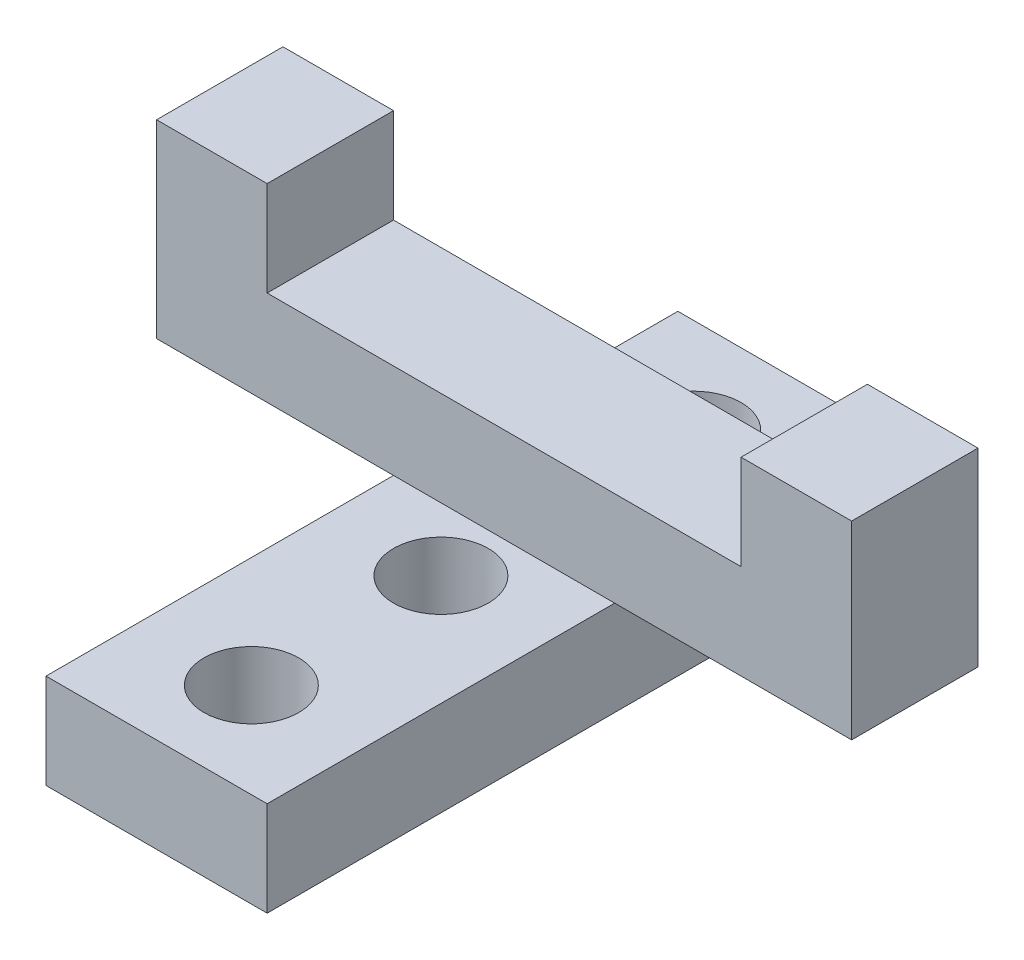
SolidWorks part; units mm, degrees
ref_plane "Front Plane" through (0, 0, 0) normal (0, 0, 1) x (1, 0, 0)
ref_plane "Top Plane" through (0, 0, 0) normal (0, 1, 0) x (1, 0, 0)
ref_plane "Right Plane" through (0, 0, 0) normal (1, 0, 0) x (0, 0, -1)
sketch "Sketch2" plane through (0, 0, 0) normal (0, 1, 0) x (1, 0, 0)
  line L1 (-3.5, -10) -> (3.5, -10)
  line L2 (-3.5, -10) -> (-3.5, 10)
  line L3 (-3.5, 10) -> (3.5, 10)
  line L4 (3.5, -10) -> (3.5, 10)
  line L5 (-3.5, -10) -> (3.5, 10) construction
  line L6 (-3.5, 10) -> (3.5, -10) construction
  point P0 (0, 0)
  dimension "D1" = 7
  dimension "D2" = 20
extrude "Extrude2" add sketch "Sketch2" along normal blind 3
sketch "Sketch3" plane through (0, 3, 0) normal (0, 1, 0) x (-1, 0, 0)
  line L0 (0, 11.4194) -> (0, -10.989) construction
hole_wizard "Ø3.0 (3) Diameter Hole1" positions "3DSketch1" profile "Sketch5" hole size "Ø3.0" standard "Ansi Metric"
sketch3d "3DSketch1"
  line L0 (0, 3, 11.4194) -> (0, 3, -10.989) construction
  line L1 (3.5, 3, -10) -> (-3.5, 3, -10) construction
  line L2 (-3.5, 3, 10) -> (3.5, 3, 10) construction
  point P0 (0, 3, 7)
  point P4 (0, 3, 1)
  point P6 (0, 3, -7)
  dimension "D1" = 3
  dimension "D2" = 3
  dimension "D3" = 6
sketch "Sketch5" plane through (0, 3, 7) normal (1, 0, 0) x (0, 0, 1)
  line L0 (0, 0) -> (0, 10.9013)
  line L1 (0, 10.9013) -> (1.5, 10)
  line L2 (1.5, 10) -> (1.5, 0)
  line L5 (1.5, 0) -> (0, 0)
  line L10 (0, 10.9013) -> (-1.5, 10) construction
  line L11 (0, -6.35) -> (0, 107.95) construction
  dimension "Hole Dia." = 3
  dimension "Hole Depth" = 10
  dimension "Drill Angle" = 118
sketch "Sketch6" plane through (0, 3, 0) normal (0, 1, 0) x (1, 0, 0)
  line L0 (-3.5, 10) -> (-3.5, -10) construction
  line L1 (-3.5, 5) -> (3.5, 5)
  line L2 (-3.5, 5) -> (-3.5, 1)
  line L3 (-3.5, 1) -> (3.5, 1)
  line L4 (3.5, 5) -> (3.5, 1)
  line L5 (3.5, -10) -> (3.5, 10) construction
  line L6 (3.5, 10) -> (-3.5, 10) construction
  dimension "D1" = 5
  dimension "D2" = 4
extrude "Extrude3" add sketch "Sketch6" along normal blind 6
sketch "Sketch7" plane through (3.5, 0, 0) normal (1, 0, 0) x (0, 0, -1)
  line L1 (1, 3) -> (5, 3)
  line L2 (1, 3) -> (1, 9)
  line L3 (1, 9) -> (5, 9)
  line L4 (5, 3) -> (5, 9)
extrude "Extrude4" add sketch "Sketch7" along normal blind 7.5
sketch "Sketch8" plane through (-3.5, 0, 0) normal (-1, 0, 0) x (0, 0, 1)
  line L1 (-1, 3) -> (-5, 3)
  line L2 (-1, 3) -> (-1, 9)
  line L3 (-1, 9) -> (-5, 9)
  line L4 (-5, 3) -> (-5, 9)
extrude "Extrude5" add sketch "Sketch8" along normal blind 7.5
sketch "Sketch10" plane through (0, 9, 0) normal (0, 1, 0) x (-1, 0, 0)
  line L0 (-11, -5) -> (11, -5) construction
  line L1 (7.5, -5) -> (-7.5, -5)
  line L2 (7.5, -5) -> (7.5, -1)
  line L3 (7.5, -1) -> (-7.5, -1)
  line L4 (-7.5, -5) -> (-7.5, -1)
  line L5 (11, -1) -> (-11, -1) construction
  line L6 (11, -1) -> (11, -5) construction
  dimension "D1" = 15
  dimension "D2" = 3.5
extrude "Extrude6" cut sketch "Sketch10" against normal blind 3
